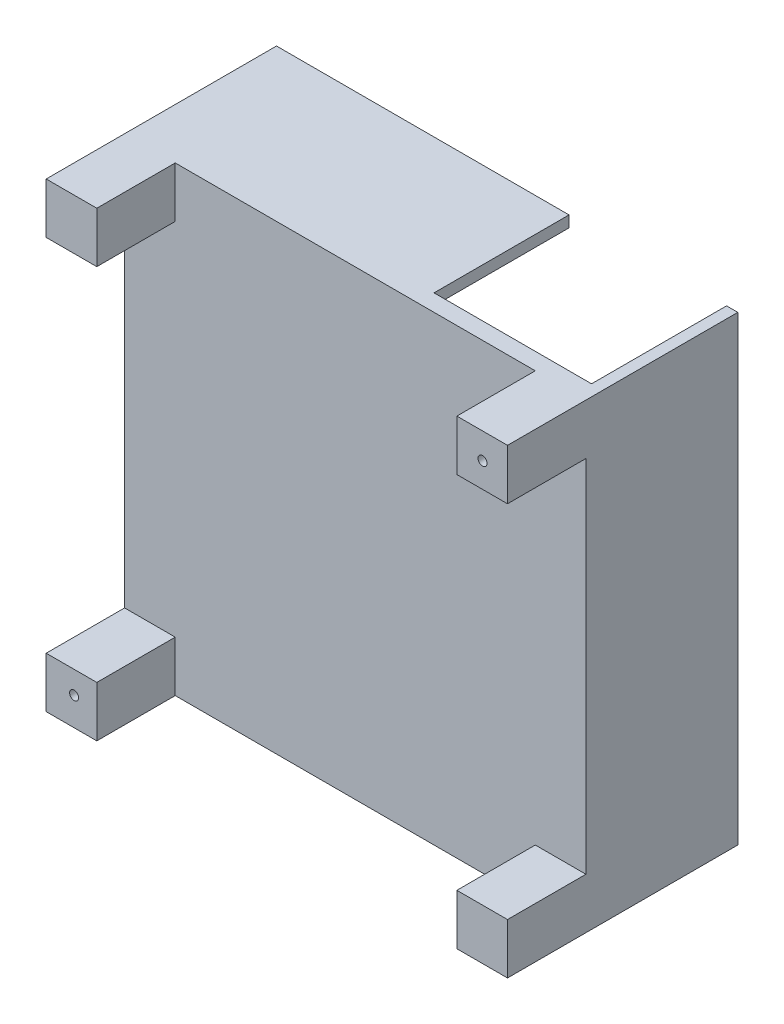
SolidWorks part; units mm, degrees
ref_plane "Piano frontale" through (0, 0, 0) normal (0, 0, 1) x (1, 0, 0)
ref_plane "Piano superiore" through (0, 0, 0) normal (0, 1, 0) x (1, 0, 0)
ref_plane "Piano destro" through (0, 0, 0) normal (1, 0, 0) x (0, 0, -1)
sketch "Schizzo1" plane through (0, 0, 0) normal (0, 0, 1) x (1, 0, 0)
  line L1 (0, 0) -> (41, 0)
  line L2 (0, 0) -> (0, 41)
  line L3 (0, 41) -> (41, 41)
  line L4 (41, 0) -> (41, 41)
  dimension "D1" = 41
  dimension "D2" = 41
extrude "Estrusione-Estrusione1" add sketch "Schizzo1" along normal blind 1.5 contours L1 L4 L3 L2
sketch "Schizzo5" plane through (0, 0, 1.5) normal (0, 0, 1) x (1, 0, 0)
  line L1 (0, 0) -> (4.5, 0)
  line L2 (0, 0) -> (0, 4.5)
  line L3 (0, 4.5) -> (4.5, 4.5)
  line L4 (4.5, 0) -> (4.5, 4.5)
  dimension "D1" = 4.5
  dimension "D2" = 4.5
extrude "Estrusione-Estrusione2" add sketch "Schizzo5" along normal blind 6.97
sketch "Schizzo6" plane through (0, 0, 1.5) normal (0, 0, 1) x (1, 0, 0)
  line L1 (41, 0) -> (36.5, 0)
  line L2 (41, 0) -> (41, 4.5)
  line L3 (41, 4.5) -> (36.5, 4.5)
  line L4 (36.5, 0) -> (36.5, 4.5)
  dimension "D1" = 4.5
  dimension "D2" = 4.5
extrude "Estrusione-Estrusione3" add sketch "Schizzo6" along normal blind 6.97
sketch "Schizzo7" plane through (0, 0, 1.5) normal (0, 0, 1) x (1, 0, 0)
  line L1 (0, 41) -> (4.5, 41)
  line L2 (0, 41) -> (0, 36.5)
  line L3 (0, 36.5) -> (4.5, 36.5)
  line L4 (4.5, 41) -> (4.5, 36.5)
  dimension "D1" = 4.5
  dimension "D2" = 4.5
extrude "Estrusione-Estrusione4" add sketch "Schizzo7" along normal blind 6.97
sketch "Schizzo8" plane through (0, 0, 1.5) normal (0, 0, 1) x (1, 0, 0)
  line L1 (41, 41) -> (36.5, 41)
  line L2 (41, 41) -> (41, 36.5)
  line L3 (41, 36.5) -> (36.5, 36.5)
  line L4 (36.5, 41) -> (36.5, 36.5)
  dimension "D1" = 4.5
  dimension "D2" = 4.5
extrude "Estrusione-Estrusione5" add sketch "Schizzo8" along normal blind 6.97
sketch "Schizzo9" plane through (0, 0, 0) normal (0, 0, -1) x (-1, 0, 0)
  line L0 (0, 0) -> (-41, 0) construction
  line L1 (-41, 41) -> (-40, 41)
  line L2 (-41, 41) -> (-41, 0)
  line L3 (-41, 0) -> (-40, 0)
  line L4 (-40, 41) -> (-40, 0)
  dimension "D1" = 1
  dimension "D2" = 41
extrude "Estrusione-Estrusione6" add sketch "Schizzo9" along normal blind 12
sketch "Schizzo10" plane through (0, 0, 0) normal (0, 0, -1) x (-1, 0, 0)
  line L0 (0, 41) -> (-40, 41) construction
  line L1 (-26, 41) -> (0, 41)
  line L2 (-26, 41) -> (-26, 40)
  line L3 (-26, 40) -> (0, 40)
  line L4 (0, 41) -> (0, 40)
  line L5 (0, 0) -> (0, 41) construction
  dimension "D1" = 26
  dimension "D2" = 1
extrude "Estrusione-Estrusione7" add sketch "Schizzo10" along normal blind 12
sketch "Schizzo11" plane through (0, 0, 8.47) normal (0, 0, 1) x (1, 0, 0)
  circle A0 centre (38.7811, 38.7) radius 0.4
  dimension "D1" = 0.8
extrude "Taglio-Estrusione1" cut sketch "Schizzo11" against normal blind 10
sketch "Schizzo12" plane through (0, 0, 8.47) normal (0, 0, 1) x (1, 0, 0)
  circle A0 centre (2.4811, 2.5) radius 0.4
  dimension "D1" = 0.8
extrude "Taglio-Estrusione2" cut sketch "Schizzo12" against normal blind 10
